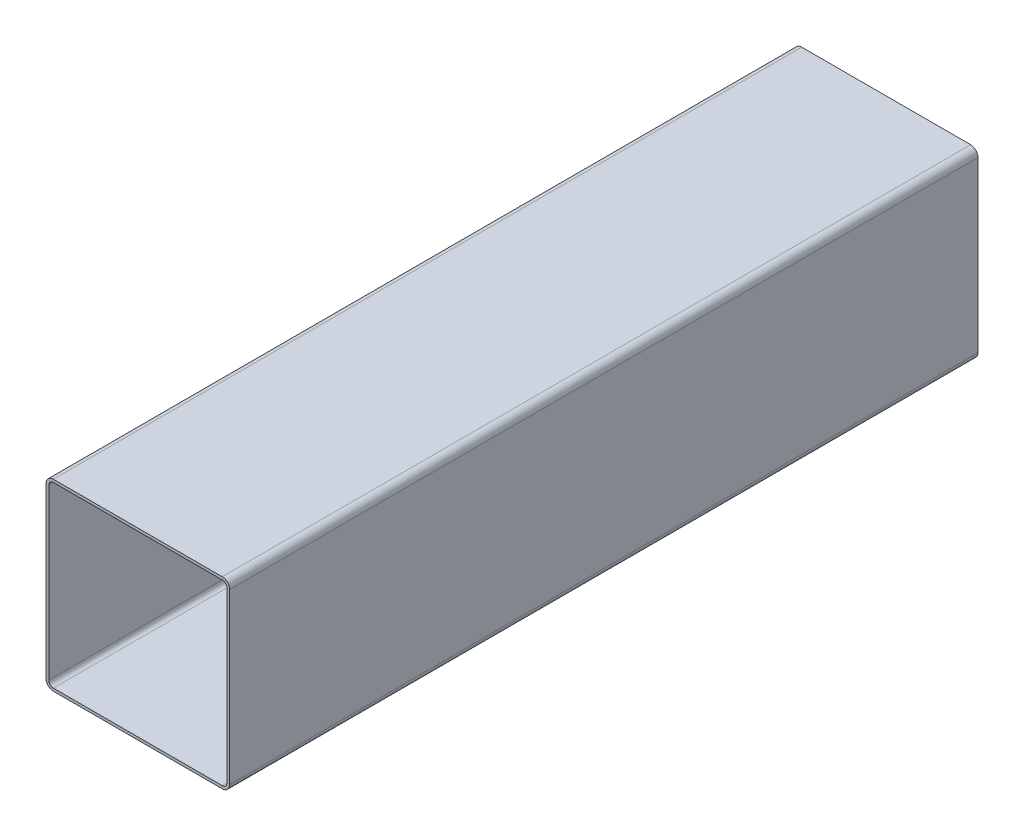
SolidWorks part; units mm, degrees
ref_plane "Спереди" through (0, 0, 0) normal (0, 0, 1) x (1, 0, 0)
ref_plane "Сверху" through (0, 0, 0) normal (0, 1, 0) x (1, 0, 0)
ref_plane "Справа" through (0, 0, 0) normal (1, 0, 0) x (0, 0, -1)
sketch "Эскиз1" plane through (0, 0, 0) normal (0, 0, 1) x (1, 0, 0)
  line L1 (92, -100) -> (-92, -100)
  line L2 (100, -92) -> (100, 92)
  line L3 (92, 100) -> (-92, 100)
  line L4 (-100, -92) -> (-100, 92)
  line L5 (100, -100) -> (-100, 100) construction
  line L6 (100, 100) -> (-100, -100) construction
  arc A0 (-100, -92) -> (-92, -100) centre (-92, -92) ccw
  arc A1 (92, -100) -> (100, -92) centre (92, -92) ccw
  arc A2 (100, 92) -> (92, 100) centre (92, 92) ccw
  arc A3 (-100, 92) -> (-92, 100) centre (-92, 92) cw
  point P0 (0, 0)
  dimension "D2" = 8
  dimension "D1" = 200
extrude "Вытянуть-Тонкостенный1" add sketch "Эскиз1" along normal blind 815 thin
